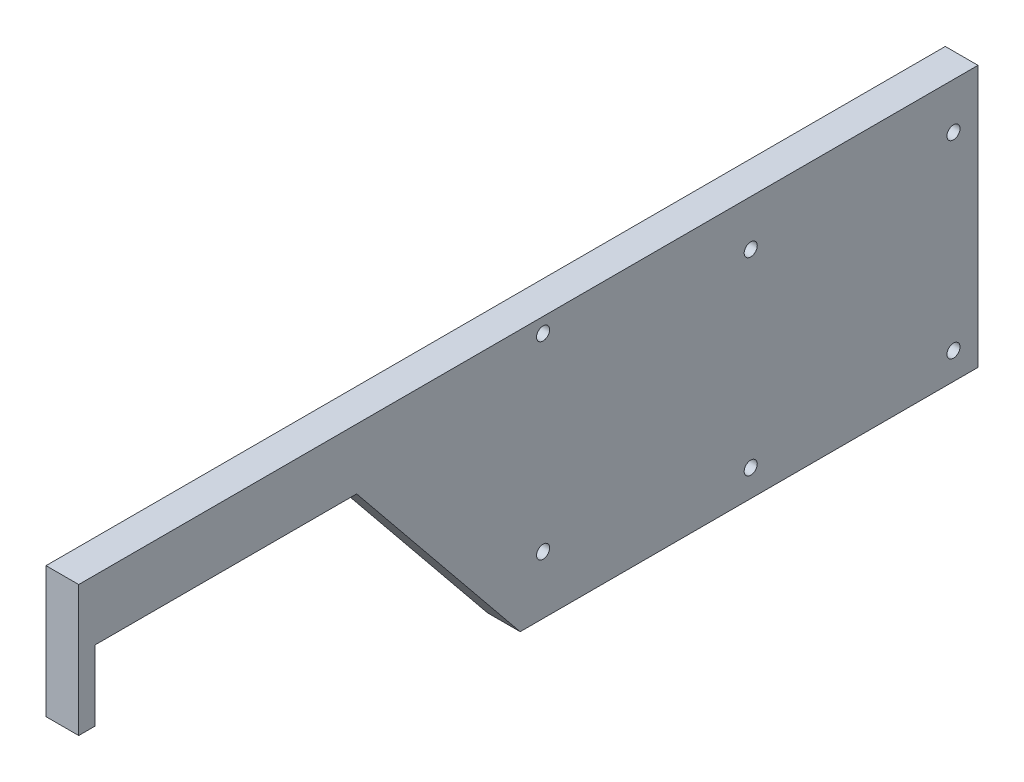
SolidWorks part; units mm, degrees
ref_plane "Front Plane" through (0, 0, 0) normal (0, 0, 1) x (1, 0, 0)
ref_plane "Top Plane" through (0, 0, 0) normal (0, 1, 0) x (1, 0, 0)
ref_plane "Right Plane" through (0, 0, 0) normal (1, 0, 0) x (0, 0, -1)
sketch "Sketch1" plane through (0, 0, 0) normal (1, 0, 0) x (0, 0, -1)
  line L0 (99, 24.75) -> (99, -33.05) construction
  line L1 (-38, -10.75) -> (38, -10.75) construction
  line L2 (-38, -10.75) -> (-38, 10.75) construction
  line L3 (-38, 10.75) -> (38, 10.75) construction
  line L4 (38, -10.75) -> (38, 10.75) construction
  line L5 (-38, -10.75) -> (38, 10.75) construction
  line L6 (-38, 10.75) -> (38, -10.75) construction
  line L7 (99, -33.05) -> (162.5, -42.55) construction
  line L8 (162.5, -42.55) -> (162.5, 15.25) construction
  line L9 (162.5, 15.25) -> (224.5, 15.25) construction
  line L10 (224.5, 15.25) -> (224.5, -42.55) construction
  line L11 (224.5, -42.55) -> (162.5, -42.55) construction
  line L12 (-38, 10.75) -> (-38, -10.75)
  line L13 (-38, -10.75) -> (-43, -10.75)
  line L14 (-43, -10.75) -> (-43, 29.25)
  line L15 (-43, 29.25) -> (232, 29.25)
  line L16 (232, 29.25) -> (232, -50.75)
  line L17 (232, -50.75) -> (92, -50.75)
  line L18 (92, -50.75) -> (42, 10.75)
  line L19 (42, 10.75) -> (-38, 10.75)
  circle A0 centre (99, 24.75) radius 2
  circle A1 centre (99, -33.05) radius 2
  circle A2 centre (162.5, 15.25) radius 2
  circle A3 centre (224.5, 15.25) radius 2
  circle A4 centre (162.5, -42.55) radius 2
  circle A5 centre (224.5, -42.55) radius 2
  point P0 (0, 0)
  point P22 (230.6794, -47.8256)
  point P27 (74.229, 14.2888)
  dimension "D3" = 4
  dimension "D1" = 76
  dimension "D2" = 21.5
  dimension "D4" = 57.8
  dimension "D5" = 9.5
  dimension "D6" = 63.5
  dimension "D7" = 61
  dimension "D8" = 14
  dimension "D9" = 62
  dimension "D10" = 5
  dimension "D11" = 40
  dimension "D12" = 80
  dimension "D13" = 140
  dimension "D14" = 80
  dimension "D15" = 50
extrude "Boss-Extrude1" add sketch "Sketch1" along normal blind 10
